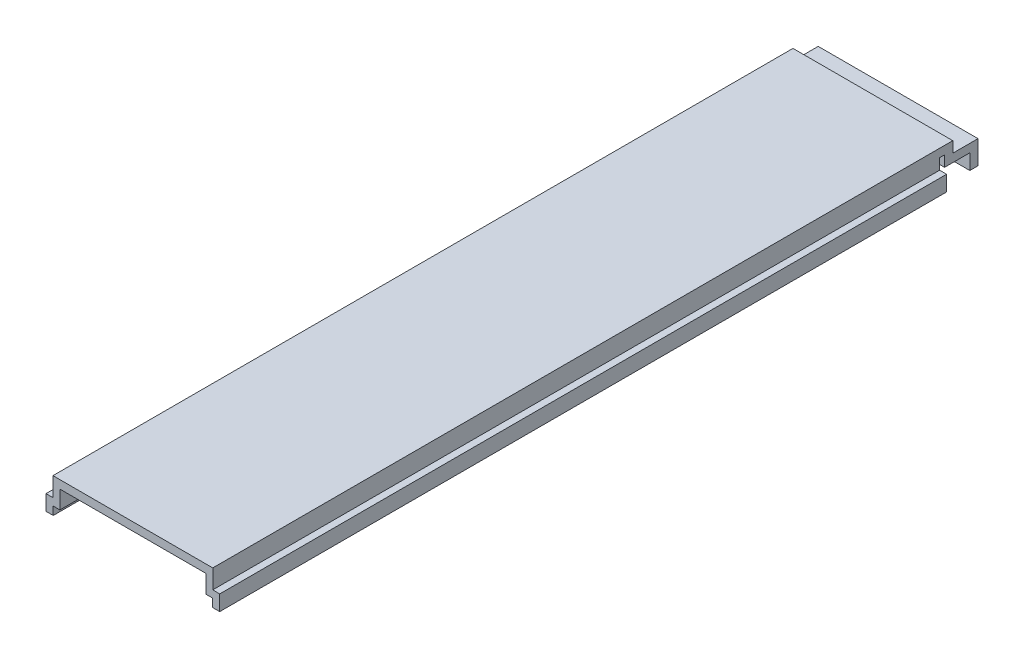
SolidWorks part; units mm, degrees
material "Plain Carbon Steel"
ref_plane "Front Plane" through (0, 0, 0) normal (0, 0, 1) x (1, 0, 0)
ref_plane "Top Plane" through (0, 0, 0) normal (0, 1, 0) x (1, 0, 0)
ref_plane "Right Plane" through (0, 0, 0) normal (1, 0, 0) x (0, 0, -1)
sketch "Sketch1" plane through (0, 0, 0) normal (0, 0, 1) x (1, 0, 0)
  line L0 (-2.36, 23.6872) -> (59.64, 23.6872)
  line L1 (-2.36, 23.6872) -> (-2.36, 16.2988)
  line L2 (-2.36, 16.2988) -> (-5.06, 16.2988)
  line L3 (-5.06, 16.2988) -> (-5.06, 10.3372)
  line L4 (59.64, 23.6872) -> (59.64, 16.2988)
  line L5 (59.64, 16.2988) -> (62.34, 16.2988)
  line L6 (62.34, 16.2988) -> (62.34, 10.3372)
  line L7 (-5.06, 10.3372) -> (-2.26, 10.3372)
  line L8 (-2.26, 10.3372) -> (-2.26, 13.5122)
  line L9 (-2.26, 13.5122) -> (0.34, 13.5122)
  line L10 (0.34, 13.5122) -> (0.34, 20.5122)
  line L11 (0.34, 20.5122) -> (56.94, 20.5122)
  line L12 (56.94, 20.5122) -> (56.94, 13.5122)
  line L13 (56.94, 13.5122) -> (59.54, 13.5122)
  line L14 (59.54, 13.5122) -> (59.54, 10.3372)
  line L15 (59.54, 10.3372) -> (62.34, 10.3372)
  dimension "D1" = 62
  dimension "D2" = 2.7
  dimension "D3" = 2.7
  dimension "D4" = 2.6
  dimension "D5" = 3.175
  dimension "D6" = 7
  dimension "D7" = 3.175
extrude "Boss-Extrude1" add sketch "Sketch1" along normal blind 282
sketch "Sketch5" plane through (-2.36, 0, 0) normal (-1, 0, 0) x (0, 0, 1)
  line L0 (0, 23.6872) -> (-5.1, 23.6872)
  line L1 (-5.1, 23.6872) -> (-5.1, 19.4738)
  line L2 (-5.1, 19.4738) -> (-14.89, 19.4738)
  line L3 (-14.89, 19.4738) -> (-14.89, 10.3372)
  line L4 (-14.89, 10.3372) -> (-11.715, 10.3372)
  line L5 (-11.715, 10.3372) -> (-11.715, 16.2988)
  line L6 (-11.715, 16.2988) -> (-1.925, 16.2988)
  line L7 (-1.925, 16.2988) -> (-1.925, 20.5122)
  line L8 (-1.925, 20.5122) -> (0, 20.5122)
  line L9 (0, 23.6872) -> (0, 16.2988) construction
  line L10 (0, 23.6872) -> (0, 20.5122)
  line L11 (282, 16.2988) -> (0, 16.2988) construction
  line L12 (282, 10.3372) -> (0, 10.3372) construction
  dimension "D1" = 1.925
  dimension "D2" = 3.175
  dimension "D3" = 3.175
  dimension "D5" = 3.175
extrude "Boss-Extrude2" add sketch "Sketch5" against normal up to surface (62 mm away) up to face at (59.64, 19.993, 141)
